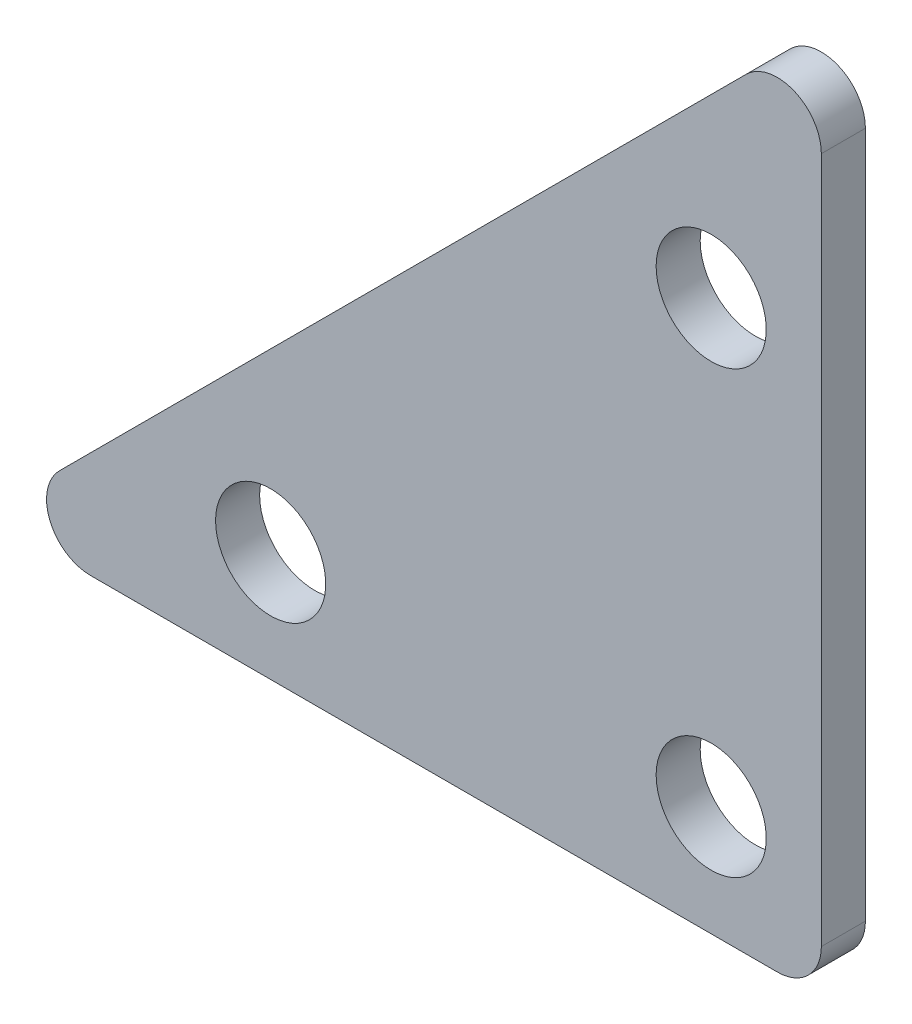
SolidWorks part; units mm, degrees
ref_plane "Front Plane" through (0, 0, 0) normal (0, 0, 1) x (1, 0, 0)
ref_plane "Top Plane" through (0, 0, 0) normal (0, 1, 0) x (1, 0, 0)
ref_plane "Right Plane" through (0, 0, 0) normal (1, 0, 0) x (0, 0, -1)
sketch "Sketch1" plane through (0, 0, 0) normal (0, 0, 1) x (1, 0, 0)
  line L0 (0, 0) -> (0, 38)
  line L1 (0, 38) -> (-38, 0)
  line L2 (-38, 0) -> (0, 0)
  point P3 (-5, 5)
  point P5 (-25, 5)
  point P6 (-5, 25)
  dimension "D1" = 38
  dimension "D2" = 38
  dimension "D3" = 5
  dimension "D4" = 5
  dimension "D5" = 20
  dimension "D6" = 20
extrude "Boss-Extrude1" add sketch "Sketch1" along normal blind 2
hole_wizard "Ø5.0mm Dowel Hole1" positions "Sketch4" profile "Sketch5" hole size "Ø5.0" standard "ANSI Metric" end condition through all
sketch "Sketch4" plane through (0, 0, 0) normal (0, 0, -1) x (-1, 0, 0)
  point P0 (5, 25)
  point P3 (5, 5)
  point P6 (25, 5)
sketch "Sketch5" plane through (-5, 25, 0) normal (1, 0, 0) x (0, 1, 0)
  line L0 (0, 0) -> (0, 2)
  line L1 (0, 2) -> (2.5, 2)
  line L2 (2.5, 2) -> (2.5, 0)
  line L5 (2.5, 0) -> (0, 0)
  line L11 (0, -6.35) -> (0, 107.95) construction
  dimension "Thru Hole Dia." = 5
  dimension "Thru Hole Depth" = 2
fillet "Fillet1" radius 2 3 edges at (0, 0, 1) (0, 38, 1) (-38, 0, 1)
